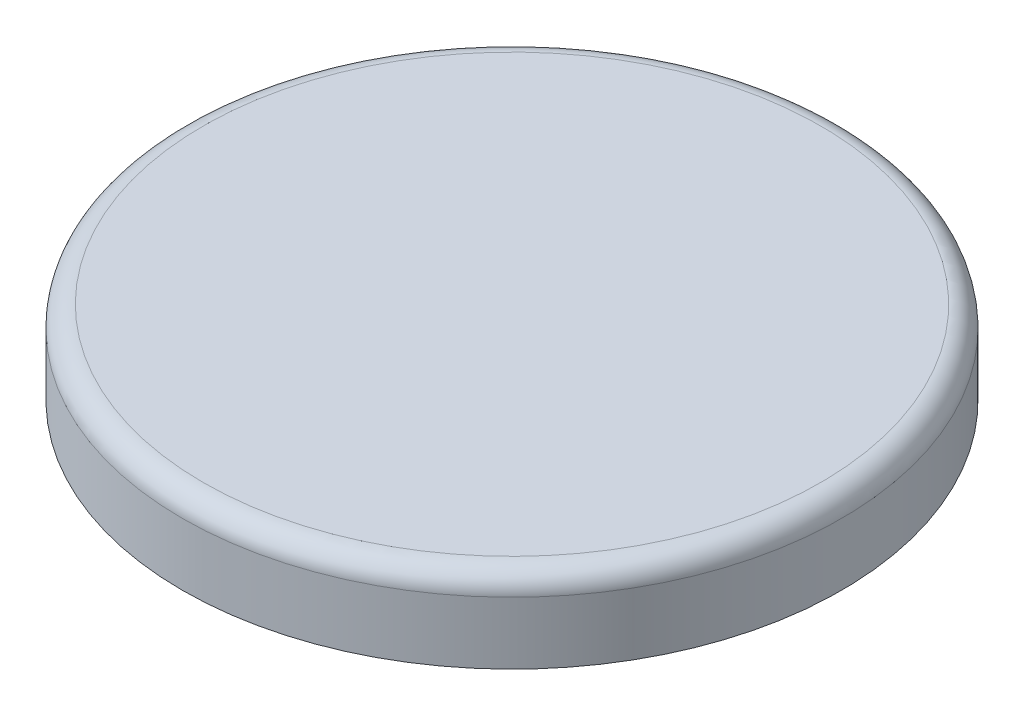
SolidWorks part; units mm, degrees
ref_plane "Front Plane" through (0, 0, 0) normal (0, 0, 1) x (1, 0, 0)
ref_plane "Top Plane" through (0, 0, 0) normal (0, 1, 0) x (1, 0, 0)
ref_plane "Right Plane" through (0, 0, 0) normal (1, 0, 0) x (0, 0, -1)
sketch "Sketch1" plane through (0, 0, 0) normal (0, 1, 0) x (1, 0, 0)
  circle A2 centre (0, 0) radius 3.175
  dimension "D1" = 6.35
extrude "Boss-Extrude1" add sketch "Sketch1" along normal blind 0.8
fillet "Fillet3" radius 0.2 1 edges at (0, 0.8, 3.175)
